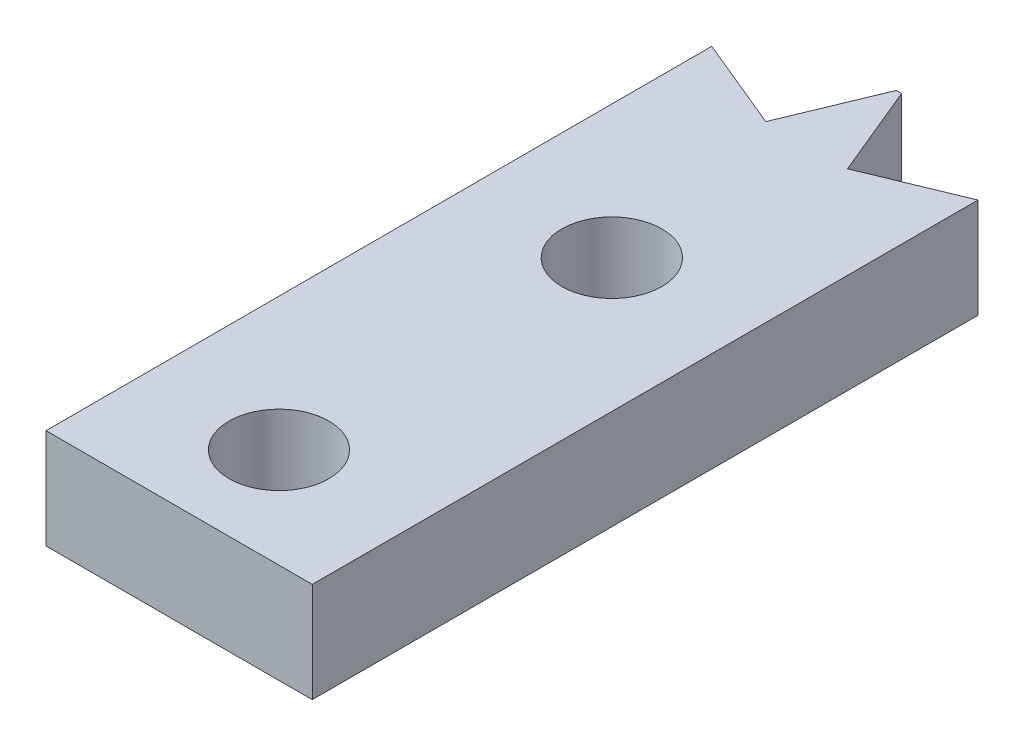
SolidWorks part; units mm, degrees
ref_plane "Front Plane" through (0, 0, 0) normal (0, 0, 1) x (1, 0, 0)
ref_plane "Top Plane" through (0, 0, 0) normal (0, 1, 0) x (1, 0, 0)
ref_plane "Right Plane" through (0, 0, 0) normal (1, 0, 0) x (0, 0, -1)
sketch "Sketch1" plane through (0, 0, 0) normal (0, 1, 0) x (1, 0, 0)
  line L0 (-3.2723, -0.8008) -> (-2.1242, 1.9709)
  line L1 (1.9555, 0.3473) -> (-0.8162, -0.8008)
  line L4 (-0.8162, -0.8008) -> (-1.9642, 1.9709)
  line L5 (-1.9642, 1.9709) -> (-2.1242, 1.9709)
  line L15 (-6.0439, 0.3473) -> (-3.2723, -0.8008)
  line L16 (-6.0439, -4.7777) -> (-6.0439, 0.3473)
  line L24 (1.9555, 0.3473) -> (1.9555, -17.1527)
  line L32 (-6.0439, -17.2777) -> (-6.0439, -4.7777)
  line L35 (-6.0439, -17.2777) -> (-6.0439, -19.6535)
  line L36 (-6.0439, -19.6535) -> (1.9555, -19.6535)
  line L37 (1.9555, -17.1527) -> (1.9555, -19.6535)
  circle A0 centre (-2.0445, -6.6535) radius 1.5021
  circle A1 centre (-2.0445, -16.6535) radius 1.5002
  dimension "D6" = 4
  dimension "D7" = 4
  dimension "D9" = 3
  dimension "D10" = 10
  dimension "D5" = 3
  dimension "D12" = 1.8758
  dimension "D1" = 3
  dimension "D2" = 3
  dimension "D3" = 0.16
  dimension "D4" = 7.9994
  dimension "D8" = 12.5
  dimension "D11" = 3
extrude "Boss-Extrude3" add sketch "Sketch1" along normal blind 3
sketch "Sketch4" plane through (0, 3, 0) normal (0, 1, 0) x (1, 0, 0)
  line L0 (-6.0439, 0.3473) -> (-6.0439, -19.6535) construction
  circle A0 centre (-4.0439, -11.6535) radius 0.9953
  circle A1 centre (-0.0439, -11.6535) radius 0.9953
  circle A2 centre (-2.0445, -6.6535) radius 1.5021 construction
  dimension "D2" = 2
  dimension "D3" = 5
  dimension "D1" = 2
sketch "Sketch5" plane through (0, 0, -1.9709) normal (0, 0, -1) x (-1, 0, 0)
  line L1 (1.9642, 3) -> (1.9642, 0) construction
  line L2 (1.9642, 0) -> (2.1242, 0) construction
  circle A1 centre (2.0442, 1.5) radius 0.05
  dimension "D1" = 0.08
  dimension "D2" = 1.5
hole_wizard "Ø2.0mm Dowel Hole2" positions "Sketch10" profile "Sketch11" hole size "Ø2.0" standard "ANSI Metric"
sketch "Sketch10" plane through (0, 3, 0) normal (0, 1, 0) x (1, 0, 0)
  point P0 (-4.0439, -11.6535)
  point P3 (-0.0439, -11.6535)
sketch "Sketch11" plane through (-4.0439, 3, 11.6535) normal (1, 0, 0) x (0, 0, 1)
  line L0 (0, 0) -> (0, 3)
  line L1 (0, 3) -> (1, 3)
  line L2 (1, 3) -> (1, 0)
  line L5 (1, 0) -> (0, 0)
  line L11 (0, -6.35) -> (0, 107.95) construction
  dimension "Thru Hole Dia." = 2
  dimension "Thru Hole Depth" = 3
sketch "Sketch12" plane through (0, 0, -1.9709) normal (0, 0, -1) x (-1, 0, 0)
  line L0 (1.9642, 3) -> (2.1242, 3) construction
  line L2 (1.9642, 3) -> (1.9642, 0) construction
  circle A0 centre (2.0442, 1.5) radius 0.0582
  dimension "D1" = 1.5
  dimension "D2" = 0.08
